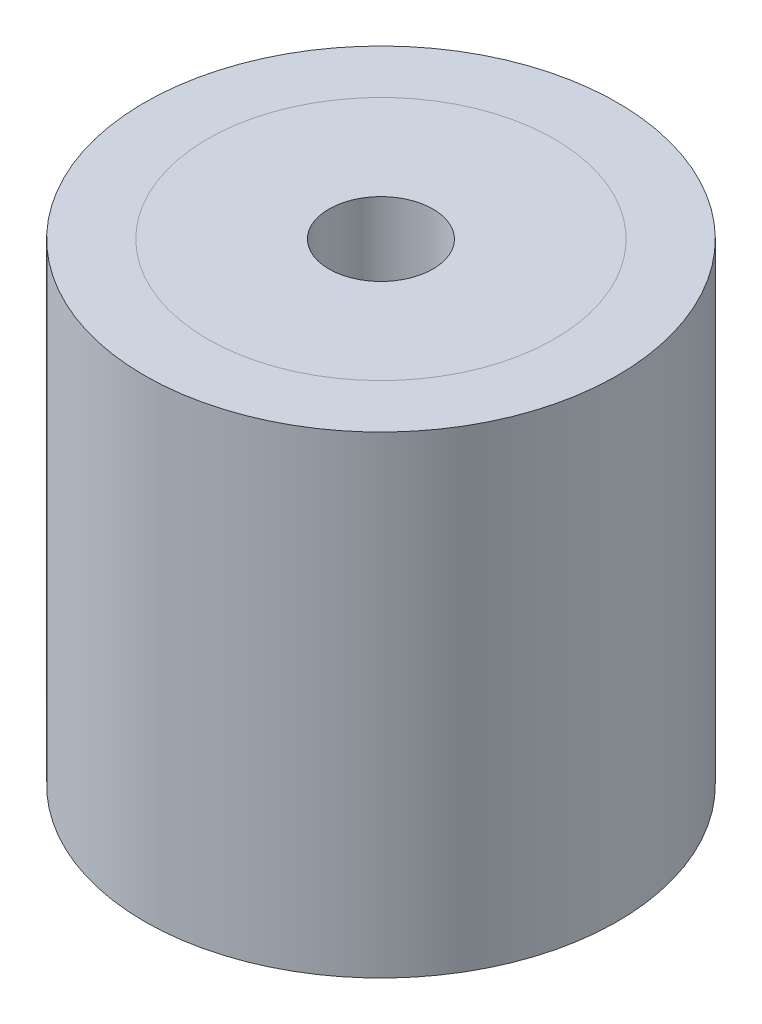
SolidWorks part; units mm, degrees
material "6061 合金"
ref_plane "前视基准面" through (0, 0, 0) normal (0, 0, 1) x (1, 0, 0)
ref_plane "上视基准面" through (0, 0, 0) normal (0, 1, 0) x (1, 0, 0)
ref_plane "右视基准面" through (0, 0, 0) normal (1, 0, 0) x (0, 0, -1)
sketch "草图1" plane through (0, 0, 0) normal (0, 1, 0) x (1, 0, 0)
  circle A0 centre (0, 0) radius 7.5
  dimension "D1" = 15
extrude "凸台-拉伸1" add sketch "草图1" along normal mid plane 15
hole_wizard "M4 螺纹孔1" positions "草图3" profile "草图4" tap size "M4" standard "GB"
sketch "草图3" plane through (0, 7.5, 0) normal (0, 1, 0) x (1, 0, 0)
  point P0 (0, 0)
sketch "草图4" plane through (0, 7.5, 0) normal (1, 0, 0) x (0, 0, 1)
  line L0 (0, 0) -> (0, 22.4914)
  line L1 (0, 22.4914) -> (1.65, 21.5)
  line L2 (1.65, 21.5) -> (1.65, 0)
  line L5 (1.65, 0) -> (0, 0)
  line L10 (0, 22.4914) -> (-1.65, 21.5) construction
  line L11 (0, -6.35) -> (0, 107.95) construction
  dimension "螺纹孔钻头直径" = 3.3
  dimension "螺纹孔钻头深度" = 21.5
  dimension "导头角度" = 118
cosmetic thread "孔螺蚊线1" parameters "D1"=8, "D2"=4
sketch "草图5" plane through (0, 7.5, 0) normal (0, 1, 0) x (1, 0, 0)
  circle A0 centre (0, 0) radius 5.5
  dimension "D1" = 11
split line "分割线1"
